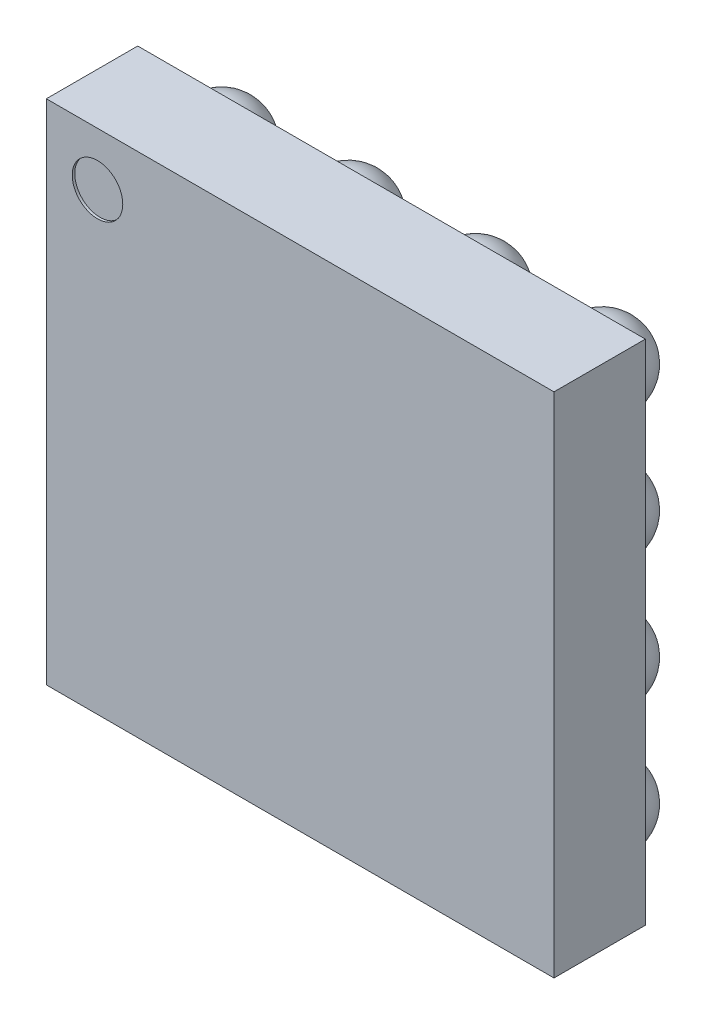
SolidWorks part; units mm, degrees
ref_plane "Front Plane" through (0, 0, 0) normal (0, 0, 1) x (1, 0, 0)
ref_plane "Top Plane" through (0, 0, 0) normal (0, 1, 0) x (1, 0, 0)
ref_plane "Right Plane" through (0, 0, 0) normal (1, 0, 0) x (0, 0, -1)
sketch "Sketch1" plane through (0, 0, 0) normal (0, 0, 1) x (1, 0, 0)
  line L1 (-1, -1) -> (1, -1)
  line L2 (-1, -1) -> (-1, 1)
  line L3 (-1, 1) -> (1, 1)
  line L4 (1, -1) -> (1, 1)
  line L5 (-1, -1) -> (1, 1) construction
  line L6 (-1, 1) -> (1, -1) construction
  point P0 (0, 0)
  dimension "D1" = 2
  dimension "D2" = 2
extrude "Boss-Extrude1" add sketch "Sketch1" along normal blind 0.36 from offset 0.24
ref_plane "Plane1" through (0.75, 0, 0) normal (1, 0, 0) x (0, 0, -1)
sketch "Sketch2" plane through (0.75, 0, 0) normal (1, 0, 0) x (0, 0, -1)
  line L0 (-0.32, 0.75) -> (0, 0.75)
  arc A0 (-0.32, 0.75) -> (0, 0.75) centre (-0.16, 0.75) ccw
  dimension "D1" = 0.16
  dimension "D2" = 0.75
revolve "Revolve1" add sketch "Sketch2" angle 360 about L0
pattern_linear "LPattern1" count 4 spacing 0.5 along (-1, 0, 0) count 4 spacing 0.5 along (0, -1, 0) of "Revolve1"
sketch "Sketch3" plane through (0, 0, 0.6) normal (0, 0, 1) x (1, 0, 0)
  circle A0 centre (-0.7986, 0.7906) radius 0.0996
  point P2 (-0.7986, 0.7906)
extrude "Cut-Extrude1" cut sketch "Sketch3" against normal blind 0.01
